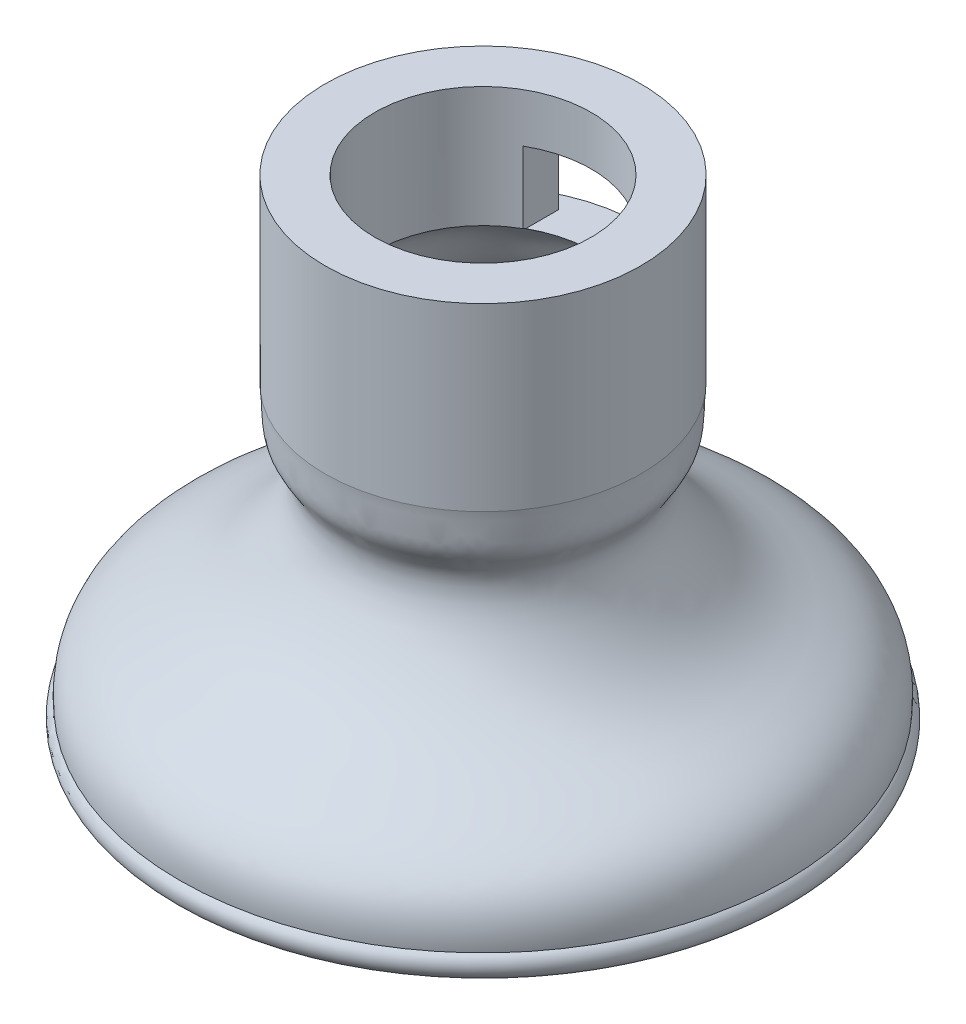
SolidWorks part; units mm, degrees
ref_plane "Plano frontal" through (0, 0, 0) normal (0, 0, 1) x (1, 0, 0)
ref_plane "Plano superior" through (0, 0, 0) normal (0, 1, 0) x (1, 0, 0)
ref_plane "Plano direito" through (0, 0, 0) normal (1, 0, 0) x (0, 0, -1)
sketch "Esboço1" plane through (0, 0, 0) normal (0, 0, 1) x (1, 0, 0)
  line L1 (12.5, 41.6466) -> (12.5, 41.5061)
  line L2 (8.5759, 46.237) -> (8.5759, 55.7804)
  line L3 (0, 44.5174) -> (0, 20.7069) construction
  line L4 (0, -55) -> (0, 55) construction
  line L5 (8.5759, 55.7804) -> (12.5, 55.7804)
  line L6 (12.5, 46.237) -> (12.5, 55.7804)
  line L7 (12.5, 46.237) -> (12.5, 41.6466)
  arc A0 (22.8518, 19.5133) -> (24.0468, 19.4039) centre (23.365, 18.537) ccw
  spline S0 degree 3 poles (12.5, 41.5061) (12.3384, 40.1348) (12.6018, 38.3052) (10.0652, 35.6456) (12.5007, 30.4583) (16.8431, 26.6707) (22.7623, 24.5329) (24.2248, 21.3493) (24.0468, 19.4039) knots 0 0 0 0 0.101005 0.17504 0.372875 0.603292 0.835962 1 1 1 1
  spline S1 degree 1 poles (11.3082, 41.6466) (22.8518, 19.5133) knots 0 0 1 1 construction
  spline S2 degree 3 poles (11.3082, 41.6466) (11.2818, 41.4218) (11.2413, 40.9533) (11.2071, 40.1531) (11.1884, 39.3253) (11.1012, 38.801) (10.9992, 38.5429) (10.8465, 38.2694) (10.6289, 37.9423) (10.3689, 37.5548) (10.0923, 37.0838) (9.7892, 36.3301) (9.6513, 35.387) (9.7889, 33.9192) (10.4316, 32.2265) (11.5346, 30.4325) (12.7309, 28.9155) (14.0632, 27.6129) (15.5166, 26.5118) (17.1175, 25.5758) (18.737, 24.7832) (20.231, 24.0091) (21.467, 23.1764) (22.1864, 22.4072) (22.5755, 21.7085) (22.7801, 21.1115) (22.8701, 20.5167) (22.8828, 19.9742) (22.8656, 19.6632) (22.8518, 19.5133) knots 0 0 0 0 0.015625 0.03125 0.0625 0.09375 0.109375 0.125 0.140625 0.15625 0.171875 0.1875 0.21875 0.25 0.3125 0.375 0.4375 0.5 0.5625 0.625 0.6875 0.75 0.8125 0.875 0.90625 0.9375 0.96875 0.984375 1 1 1 1
  spline S3 degree 3 poles (11.3082, 41.6466) (10.4882, 43.2413) (10.3327, 45.2958) (8.5759, 46.237) knots 0 0 0 0 1 1 1 1
  dimension "D1" = 1.2
revolve "Revolução1" add sketch "Esboço1" angle 360 about L3
sketch "Esboço2" plane through (0, 0, 0) normal (0, 0, 1) x (1, 0, 0)
  line L0 (0, -21.0905) -> (0, 21.0905) construction
  line L1 (4.2604, 46.1353) -> (-4.2604, 46.1353)
  line L2 (4.2604, 46.1353) -> (4.2604, 51.8993)
  line L3 (4.2604, 51.8993) -> (-4.2604, 51.8993)
  line L4 (-4.2604, 46.1353) -> (-4.2604, 51.8993)
  line L5 (4.2604, 46.1353) -> (-4.2604, 51.8993) construction
  line L6 (4.2604, 51.8993) -> (-4.2604, 46.1353) construction
  point P0 (0, 49.0173)
extrude "Corte-extrusão1" cut sketch "Esboço2" against normal blind 21
sketch "Esboço3" plane through (0, 0, 0) normal (1, 0, 0) x (0, 0, -1)
  line L1 (12.5, 51.8993) -> (10.2498, 51.8993)
  line L2 (12.5, 51.8993) -> (12.5, 46.1353)
  line L3 (12.5, 46.1353) -> (10.2498, 46.1353)
  line L4 (10.2498, 51.8993) -> (10.2498, 46.1353)
extrude "Corte-extrusão2" cut sketch "Esboço3" against normal blind 21 and the other way blind 21
